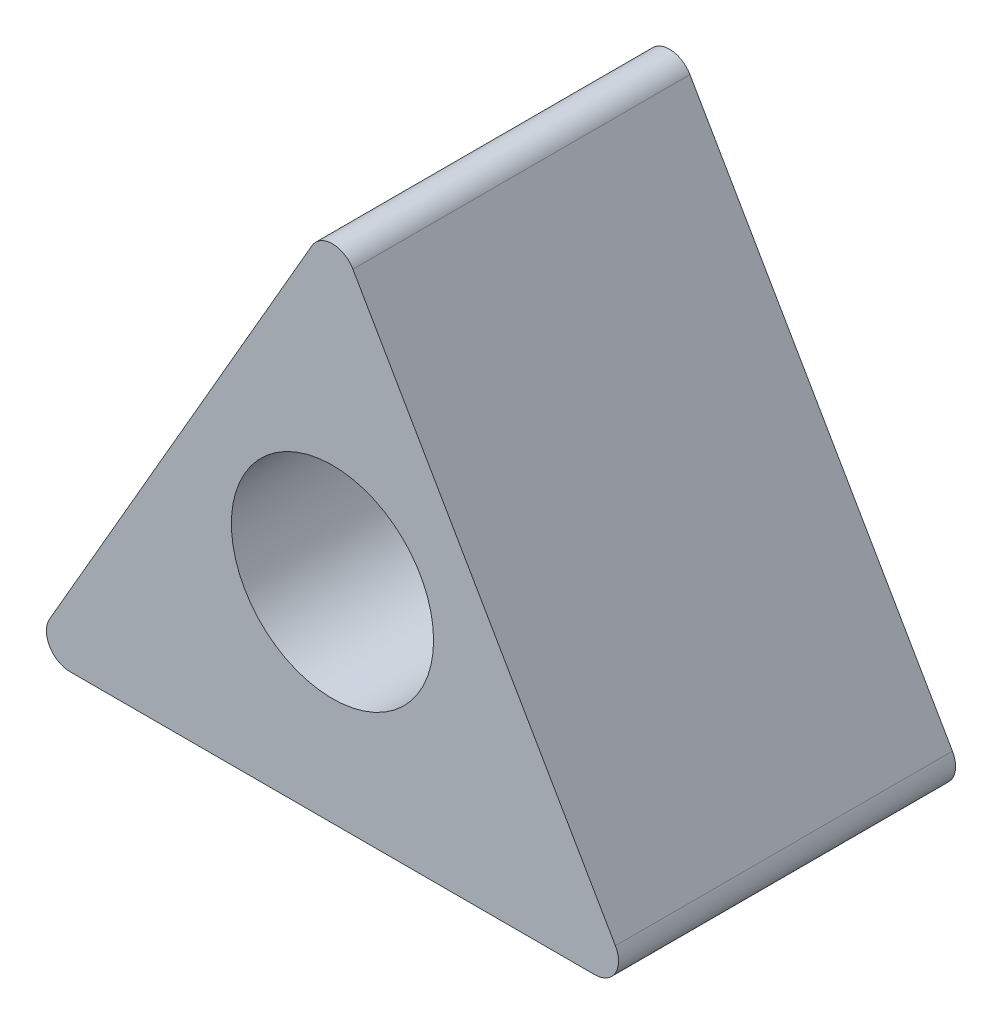
SolidWorks part; units mm, degrees
ref_plane "Front Plane" through (0, 0, 0) normal (0, 0, 1) x (1, 0, 0)
ref_plane "Top Plane" through (0, 0, 0) normal (0, 1, 0) x (1, 0, 0)
ref_plane "Right Plane" through (0, 0, 0) normal (1, 0, 0) x (0, 0, -1)
sketch "Sketch1" plane through (0, 0, 0) normal (0, 0, 1) x (1, 0, 0)
  line L6 (0, 0) -> (90, 0.0011)
  line L7 (0, 0) -> (44.999, 77.9428)
  line L8 (44.999, 77.9428) -> (90, 0.0011)
  circle A0 centre (45, 31) radius 15
extrude "Boss-Extrude2" add sketch "Sketch1" along normal blind 50
fillet "Fillet1" radius 3.5 1 edges at (44.999, 77.9428, 25)
fillet "Fillet2" radius 3.5 1 edges at (90, 0.0011, 25)
fillet "Fillet3" radius 3.5 1 edges at (0, 0, 25)
